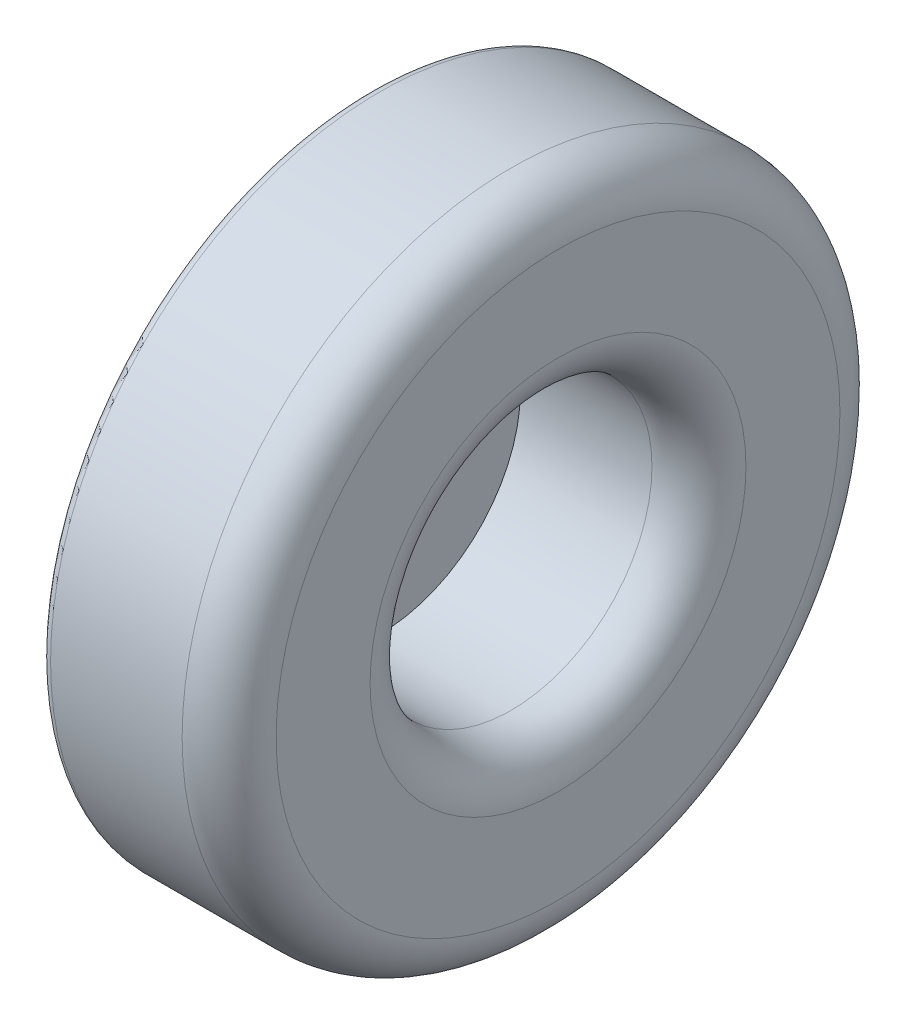
SolidWorks part; units mm, degrees
ref_plane "Front Plane" through (0, 0, 0) normal (0, 0, 1) x (1, 0, 0)
ref_plane "Top Plane" through (0, 0, 0) normal (0, 1, 0) x (1, 0, 0)
ref_plane "Right Plane" through (0, 0, 0) normal (1, 0, 0) x (0, 0, -1)
sketch "Sketch1" plane through (0, 0, 0) normal (1, 0, 0) x (0, 0, -1)
  circle A0 centre (0, 0) radius 35
  dimension "D1" = 70
extrude "Boss-Extrude1" add sketch "Sketch1" along normal blind 20
sketch "Sketch2" plane through (20, 0, 0) normal (1, 0, 0) x (0, 0, -1)
  circle A0 centre (0, 0) radius 15
  dimension "D1" = 30
extrude "Cut-Extrude1" cut sketch "Sketch2" against normal blind 19
fillet "Fillet1" radius 5 2 edges at (20, 0, -35) (20, 0, -15)
fillet "Fillet2" radius 1 1 edges at (0, 0, -35)
ref_plane "Plane2" through (0, 0, 0) normal (0, 1, 0) x (1, 0, 0)
